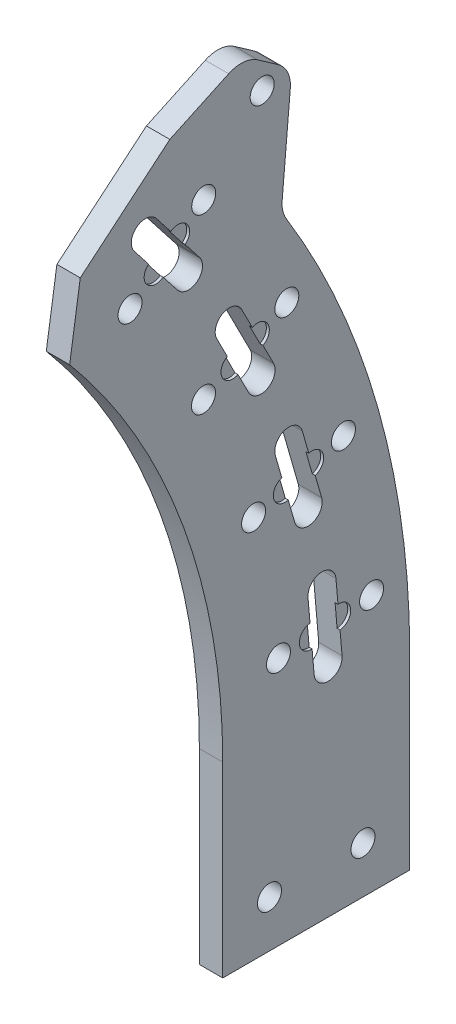
SolidWorks part; units mm, degrees
material "6061-T6 (SS)"
ref_plane "Front Plane" through (0, 0, 0) normal (0, 0, 1) x (1, 0, 0)
ref_plane "Top Plane" through (0, 0, 0) normal (0, 1, 0) x (1, 0, 0)
ref_plane "Right Plane" through (0, 0, 0) normal (1, 0, 0) x (0, 0, -1)
sketch "Sketch1" plane through (0, 0, 0) normal (1, 0, 0) x (0, 0, -1)
  line L0 (0, 0) -> (177.8, 0) construction
  line L1 (0, 0) -> (136.2027, 114.2876) construction
  line L2 (177.8, 0) -> (177.8, -50.8)
  line L3 (177.8, -50.8) -> (228.6, -50.8)
  line L4 (228.6, -50.8) -> (228.6, 0)
  line L5 (136.2027, 114.2876) -> (175.1178, 146.9412) construction
  line L6 (177.8, 0) -> (228.6, 0) construction
  line L7 (136.2027, 114.2876) -> (175.1178, 146.9412) construction
  line L9 (0, 0) -> (0, 168.3639) construction
  line L28 (177.8, -50.8) -> (177.8, -38.1) construction
  line L29 (177.8, -38.1) -> (228.6, -38.1) construction
  line L30 (0, 0) -> (136.2027, 114.2876) construction
  line L33 (175.1178, 146.9412) -> (163.4134, 153.6988)
  line L34 (163.4134, 153.6988) -> (139.0915, 133.2903)
  line L35 (139.0915, 133.2903) -> (136.2027, 114.2876)
  arc A0 (177.8, 0) -> (136.2027, 114.2876) centre (0, 0) ccw
  arc A1 (228.6, 0) -> (175.1178, 146.9412) centre (0, 0) ccw
  circle A32 centre (190.5, -38.1) radius 3.2639
  circle A33 centre (215.9, -38.1) radius 3.2639
  point P11 (151.8201, 13.2825)
  point P24 (175.0988, 30.8746)
  dimension "D24" = 6.5278
  dimension "D25" = 6.5278
  dimension "D1" = 177.8
  dimension "D2" = 40
  dimension "D3" = 50.8
  dimension "D4" = 50.8
  dimension "D10" = 90
  dimension "D21" = 12.7
  dimension "D22" = 12.7
  dimension "D23" = 12.7
  dimension "D28" = 12.7
  dimension "D29" = 31.75
  dimension "D30" = 110
extrude "Boss-Extrude1" add sketch "Sketch1" along normal blind 6.35
sketch "Sketch5" plane through (0, 0, 0) normal (0, 0, 1) x (1, 0, 0)
  line L0 (-1000, 0) -> (49000, 0) construction
sketch "Sketch6" plane through (6.35, 0, 0) normal (1, 0, 0) x (0, 0, -1)
  line L0 (0, 0) -> (203.2, 0) construction
  line L1 (0, 0) -> (155.6602, 130.6144) construction
  line L2 (0, 0) -> (218.2414, 19.0936) construction
  line L3 (0, 0) -> (210.5884, 60.3853) construction
  line L4 (0, 0) -> (195.1973, 99.458) construction
  line L5 (0, 0) -> (172.6335, 134.876) construction
  line L6 (192.0925, 64.9905) -> (197.3434, 46.6785)
  line L7 (176.1625, 100.4494) -> (184.811, 83.4757)
  line L8 (0, 0) -> (192.938, 16.8799) construction
  line L9 (0, 0) -> (186.1724, 53.3841) construction
  line L10 (200.964, 27.1435) -> (202.6243, 8.1659)
  line L11 (208.555, 27.8076) -> (210.2153, 8.8301)
  line L12 (200.964, 27.1435) -> (208.555, 27.8076) construction
  line L13 (210.2153, 8.8301) -> (202.6243, 8.1659) construction
  line L14 (204.6682, 48.7788) -> (197.3434, 46.6785) construction
  line L16 (192.0925, 64.9905) -> (199.4173, 67.0909) construction
  line L17 (199.4173, 67.0909) -> (204.6682, 48.7788)
  line L18 (191.6005, 86.9352) -> (184.811, 83.4757) construction
  line L20 (176.1625, 100.4494) -> (182.9519, 103.9088) construction
  line L21 (182.9519, 103.9088) -> (191.6005, 86.9352)
  line L22 (171.4922, 121.897) -> (165.4876, 117.2057) construction
  line L24 (153.7592, 132.2173) -> (159.7639, 136.9086) construction
  line L25 (159.7639, 136.9086) -> (171.4922, 121.897)
  line L30 (192.0925, 64.9905) -> (197.3434, 46.6785) [skipped]
  line L31 (176.1625, 100.4494) -> (184.811, 83.4757) [skipped]
  line L33 (153.7592, 132.2173) -> (165.4876, 117.2057) [skipped]
  line L34 (153.7592, 132.2173) -> (165.4876, 117.2057)
  arc A0 (203.2, 0) -> (155.6602, 130.6144) centre (0, 0) ccw construction
  arc A1 (209.55, 0) -> (160.5246, 134.6961) centre (0, 0) ccw construction
  circle A2 centre (218.2414, 19.0936) radius 9.525 construction
  arc A3 (228.6, 0) -> (175.1178, 146.9412) centre (0, 0) ccw construction
  circle A4 centre (192.938, 16.8799) radius 9.525 construction
  circle A5 centre (192.938, 16.8799) radius 3.2639
  circle A6 centre (218.2414, 19.0936) radius 3.2639
  circle A7 centre (186.1724, 53.3841) radius 3.2639
  circle A8 centre (186.1724, 53.3841) radius 9.525 construction
  circle A9 centre (210.5884, 60.3853) radius 3.2639
  circle A10 centre (210.5884, 60.3853) radius 9.525 construction
  circle A11 centre (172.5657, 87.9266) radius 3.2639
  circle A12 centre (172.5657, 87.9266) radius 9.525 construction
  circle A13 centre (195.1973, 99.458) radius 3.2639
  circle A14 centre (195.1973, 99.458) radius 9.525 construction
  circle A15 centre (152.618, 119.2382) radius 3.2639
  circle A16 centre (152.618, 119.2382) radius 9.525 construction
  circle A17 centre (172.6335, 134.876) radius 3.2639
  circle A18 centre (172.6335, 134.876) radius 9.525 construction
  arc A20 (199.4173, 67.0909) -> (192.0925, 64.9905) centre (195.7549, 66.0407) ccw
  arc A22 (191.6005, 86.9352) -> (184.811, 83.4757) centre (188.2057, 85.2055) cw
  arc A24 (208.555, 27.8076) -> (200.964, 27.1435) centre (204.7595, 27.4755) ccw
  arc A26 (210.2153, 8.8301) -> (202.6243, 8.1659) centre (206.4198, 8.498) cw
  arc A27 (204.6682, 48.7788) -> (197.3434, 46.6785) centre (201.0058, 47.7286) cw
  arc A28 (182.9519, 103.9088) -> (176.1625, 100.4494) centre (179.5572, 102.1791) ccw
  arc A29 (171.4922, 121.897) -> (165.4876, 117.2057) centre (168.4899, 119.5513) cw
  arc A30 (159.7639, 136.9086) -> (153.7592, 132.2173) centre (156.7615, 134.5629) ccw
  dimension "D3" = 19.05
  dimension "D4" = 19.05
  dimension "D6" = 6.5278
  dimension "D7" = 6.5278
  dimension "D13" = 8.89
  dimension "D2" = 40
  dimension "D5" = 5
  dimension "D9" = 11
  dimension "D10" = 19.05
  dimension "D11" = 9.525
  dimension "D1" = 6.35
  dimension "D12" = 7.62
  dimension "D8" = 4
extrude "Cut-Extrude1" cut sketch "Sketch6" against normal through all
sketch "Sketch8" plane through (6.35, 15.5516, -177.756) normal (1, 0, 0) x (0, 0.0872, -0.9962)
  line L0 (31.75, 0) -> (34.1312, 0) construction
  line L1 (31.75, -9.525) -> (31.75, 9.525) construction
  line L2 (31.75, 3.175) -> (24.13, 3.175)
  line L3 (24.13, 9.525) -> (24.13, -9.525) construction
  line L4 (24.13, -3.175) -> (31.75, -3.175)
  arc A1 (31.75, 3.175) -> (31.75, -3.175) centre (31.75, 0) cw
  arc A2 (24.13, 3.175) -> (24.13, -3.175) centre (24.13, 0) ccw
  dimension "D1" = 3.175
  dimension "D2" = 2.3812
extrude "Cut-Extrude2" cut sketch "Sketch8" against normal blind 0.7937 and the other way blind 10.033
pattern_circular "CirPattern1" count 4 every 11 about axis through (0, 0, 0) along (1, 0, 0) of "Cut-Extrude2"
sketch "Sketch9" plane through (6.35, 0, 0) normal (1, 0, 0) x (0, 0, -1)
  line L0 (0, 0) -> (188.5123, 152.6542) construction
  line L1 (0, 0) -> (72.4364, 0) construction
  circle A0 centre (188.5123, 152.6542) radius 3.2639
  dimension "D3" = 6.5278
  dimension "D1" = 242.57
  dimension "D2" = 39
sketch "Sketch11" plane through (6.35, 0, 0) normal (1, 0, 0) x (0, 0, -1)
  line L0 (163.4134, 153.6988) -> (183.5561, 163.0915)
  line L1 (183.5561, 163.0915) -> (196.5601, 153.9859)
  line L2 (196.5601, 153.9859) -> (193.7082, 121.3882)
  line L3 (163.4134, 153.6988) -> (139.0915, 133.2903) construction
  line L10 (139.0915, 133.2903) -> (136.2027, 114.2876)
  line L11 (177.8, 0) -> (177.8, -50.8)
  line L12 (177.8, -50.8) -> (228.6, -50.8)
  line L13 (228.6, -50.8) -> (228.6, 0)
  line L14 (175.1178, 146.9412) -> (163.4134, 153.6988)
  line L15 (163.4134, 153.6988) -> (139.0915, 133.2903)
  line L16 (139.0915, 133.2903) -> (136.2027, 114.2876)
  line L17 (177.8, 0) -> (177.8, -50.8)
  line L18 (177.8, -50.8) -> (228.6, -50.8)
  line L19 (228.6, -50.8) -> (228.6, 0)
  line L20 (175.1178, 146.9412) -> (163.4134, 153.6988)
  line L21 (163.4134, 153.6988) -> (139.0915, 133.2903)
  arc A0 (228.6, 0) -> (175.1178, 146.9412) centre (0, 0) ccw construction
  arc A7 (177.8, 0) -> (136.2027, 114.2876) centre (0, 0) ccw
  arc A8 (228.6, 0) -> (175.1178, 146.9412) centre (0, 0) ccw
  arc A12 (177.8, 0) -> (136.2027, 114.2876) centre (0, 0) ccw
  arc A13 (228.6, 0) -> (175.1178, 146.9412) centre (0, 0) ccw
  dimension "D1" = 165
  dimension "D2" = 22.225
  dimension "D3" = 15.875
  dimension "D4" = 120
  dimension "D5" = 120
  dimension "D6" = 0
extrude "Boss-Extrude2" add sketch "Sketch11" against normal blind 6.35
extrude "Cut-Extrude3" cut sketch "Sketch9" against normal through all both and the other way through all
fillet "Fillet2" radius 7.9375 3 edges at (3.175, 153.9859, -196.5601) (3.175, 163.0915, -183.5561) (3.175, 121.3882, -193.7082)
